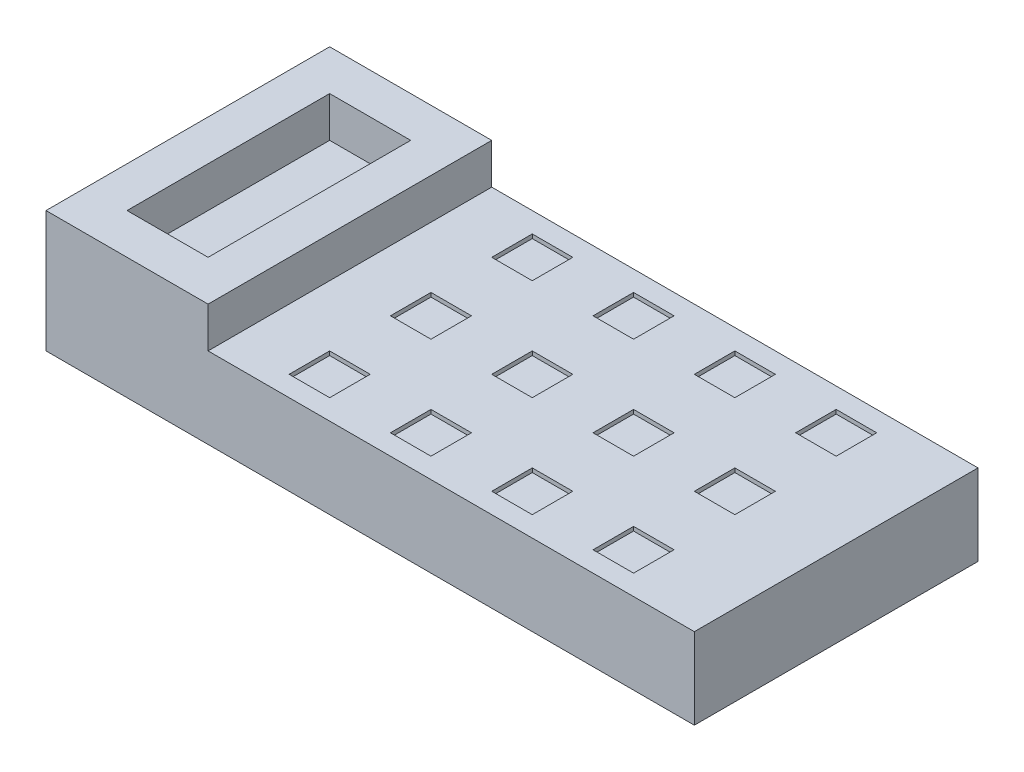
SolidWorks part; units mm, degrees
ref_plane "Front" through (0, 0, 0) normal (0, 0, 1) x (1, 0, 0)
ref_plane "Top" through (0, 0, 0) normal (0, 1, 0) x (1, 0, 0)
ref_plane "Right" through (0, 0, 0) normal (1, 0, 0) x (0, 0, -1)
sketch "Sketch1" plane through (0, 0, 0) normal (0, 1, 0) x (1, 0, 0)
  line L1 (0, 0) -> (160, 0)
  line L2 (0, 0) -> (0, 70)
  line L3 (0, 70) -> (160, 70)
  line L4 (160, 0) -> (160, 70)
extrude "Extrude1" add sketch "Sketch1" along normal blind 20
sketch "Sketch2" plane through (0, 20, 0) normal (0, 1, 0) x (-1, 0, 0)
  line L0 (-10, -10) -> (-10, -60)
  line L1 (0, 0) -> (-40, 0)
  line L2 (0, 0) -> (0, -70)
  line L3 (0, -70) -> (-40, -70)
  line L4 (-40, 0) -> (-40, -70)
  line L5 (-10, -60) -> (-30, -60)
  line L6 (-30, -10) -> (-30, -60)
  line L7 (-10, -10) -> (-30, -10)
  dimension "D1" = 70
  dimension "D2" = 40
extrude "Extrude2" add sketch "Sketch2" along normal blind 10
sketch "Sketch3" plane through (0, 20, 0) normal (0, 1, 0) x (-1, 0, 0)
  line L0 (-115, -55) -> (-105, -55)
  line L1 (-115, -65) -> (-105, -65)
  line L2 (-115, -40) -> (-105, -40)
  line L3 (-130, -30) -> (-140, -30)
  line L4 (-55, -65) -> (-55, -55)
  line L5 (-55, -15) -> (-65, -15)
  line L6 (-140, -55) -> (-130, -55)
  line L7 (-55, -5) -> (-65, -5)
  line L8 (-140, -65) -> (-130, -65)
  line L9 (-65, -65) -> (-65, -55)
  line L10 (-140, -5) -> (-140, -15)
  line L11 (-130, -5) -> (-130, -15)
  line L12 (-115, -5) -> (-115, -15)
  line L13 (-80, -5) -> (-90, -5)
  line L14 (-80, -65) -> (-80, -55)
  line L15 (-55, -30) -> (-65, -30)
  line L16 (-140, -40) -> (-130, -40)
  line L17 (-90, -65) -> (-90, -55)
  line L18 (-105, -5) -> (-105, -15)
  line L19 (-40, -5) -> (-160, -5) construction
  line L20 (-40, -15) -> (-160, -15) construction
  line L21 (-40, -30) -> (-160, -30) construction
  line L22 (-160, -40) -> (-40, -40) construction
  line L23 (-160, -55) -> (-40, -55) construction
  line L24 (-160, -65) -> (-40, -65) construction
  line L25 (-55, -70) -> (-55, 0) construction
  line L26 (-65, -70) -> (-65, 0) construction
  line L27 (-80, -15) -> (-90, -15)
  line L28 (-80, -70) -> (-80, 0) construction
  line L29 (-90, -70) -> (-90, 0) construction
  line L30 (-105, 0) -> (-105, -70) construction
  line L31 (-115, 0) -> (-115, -70) construction
  line L32 (-130, 0) -> (-130, -70) construction
  line L33 (-140, 0) -> (-140, -70) construction
  line L34 (-80, -30) -> (-90, -30)
  line L35 (-65, -40) -> (-55, -40)
  line L36 (-65, -55) -> (-55, -55)
  line L37 (-65, -65) -> (-55, -65)
  line L38 (-130, -15) -> (-140, -15)
  line L39 (-130, -5) -> (-140, -5)
  line L40 (-90, -40) -> (-80, -40)
  line L41 (-105, -30) -> (-115, -30)
  line L42 (-105, -15) -> (-115, -15)
  line L43 (-105, -5) -> (-115, -5)
  line L44 (-90, -55) -> (-80, -55)
  line L45 (-90, -65) -> (-80, -65)
  line L46 (-140, -55) -> (-140, -65)
  line L47 (-130, -55) -> (-130, -65)
  line L48 (-115, -55) -> (-115, -65)
  line L49 (-105, -55) -> (-105, -65)
  line L50 (-90, -40) -> (-90, -30)
  line L51 (-80, -40) -> (-80, -30)
  line L52 (-65, -40) -> (-65, -30)
  line L53 (-55, -40) -> (-55, -30)
  line L54 (-55, -15) -> (-55, -5)
  line L55 (-65, -15) -> (-65, -5)
  line L56 (-80, -15) -> (-80, -5)
  line L57 (-90, -15) -> (-90, -5)
  line L58 (-105, -30) -> (-105, -40)
  line L59 (-115, -30) -> (-115, -40)
  line L60 (-130, -30) -> (-130, -40)
  line L61 (-140, -30) -> (-140, -40)
extrude "Cut-Extrude1" cut sketch "Sketch3" against normal blind 1
